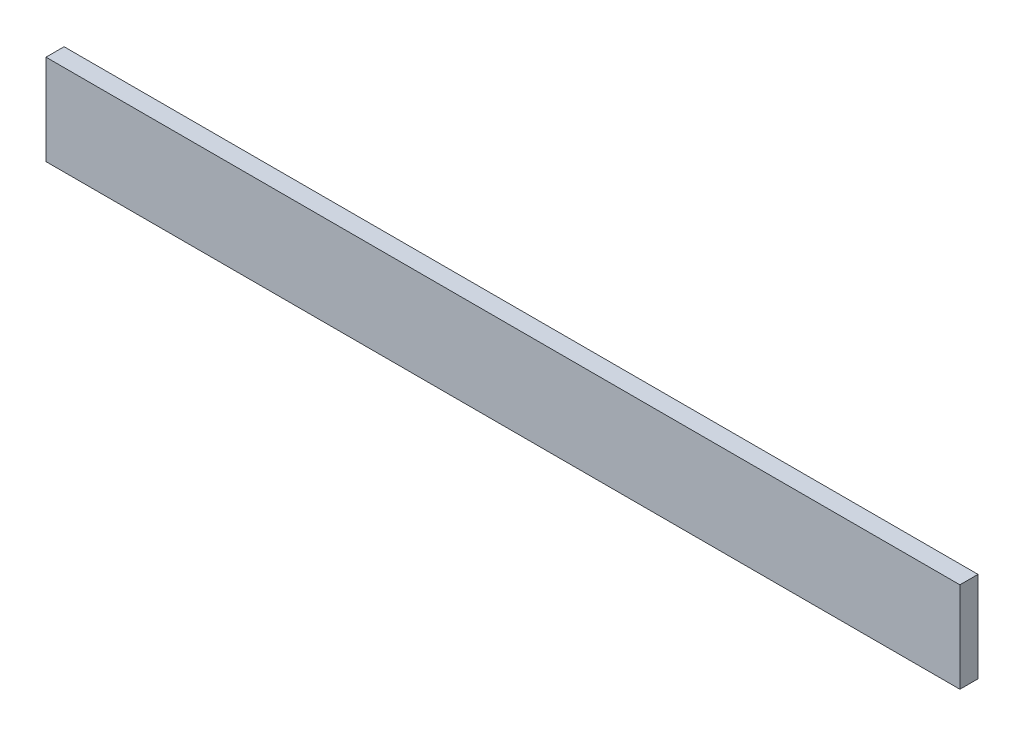
SolidWorks part; units mm, degrees
ref_plane "Спереди" through (0, 0, 0) normal (0, 0, 1) x (1, 0, 0)
ref_plane "Сверху" through (0, 0, 0) normal (0, 1, 0) x (1, 0, 0)
ref_plane "Справа" through (0, 0, 0) normal (1, 0, 0) x (0, 0, -1)
sketch "Эскиз1" plane through (0, 0, 0) normal (0, 0, 1) x (1, 0, 0)
  line L1 (0, 0) -> (505, 0)
  line L2 (0, 0) -> (0, 50)
  line L3 (0, 50) -> (505, 50)
  line L4 (505, 0) -> (505, 50)
extrude "Бобышка-Вытянуть1" add sketch "Эскиз1" along normal blind 10
